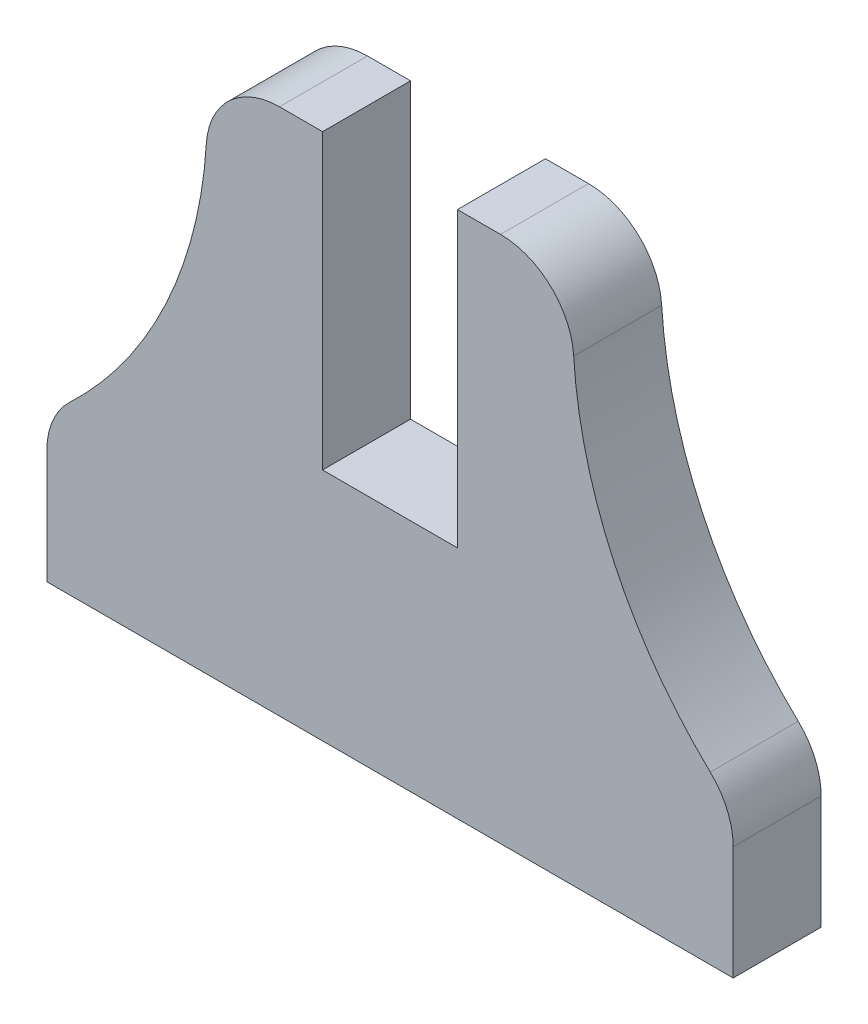
SolidWorks part; units mm, degrees
ref_plane "Front Plane" through (0, 0, 0) normal (0, 0, 1) x (1, 0, 0)
ref_plane "Top Plane" through (0, 0, 0) normal (0, 1, 0) x (1, 0, 0)
ref_plane "Right Plane" through (0, 0, 0) normal (1, 0, 0) x (0, 0, -1)
sketch "Sketch1" plane through (0, 0, 0) normal (0, 0, 1) x (1, 0, 0)
  line L0 (-4, -181.6843) -> (0, -181.6843) construction
  line L2 (-4.3, -163.6943) -> (-4.3, -173.6843)
  line L3 (-3.7, -181.6843) -> (-0.3, -181.6843)
  line L4 (0.3, -163.6943) -> (0.3, -173.6843)
  line L5 (-2, -163.6843) -> (-2, -121.6843) construction
  line L6 (-4, -121.6843) -> (0, -121.6843) construction
  line L7 (0, -171.6843) -> (0, -124.1843) construction
  line L8 (-0.3, -181.6843) -> (9.7, -181.6843)
  line L9 (0.3, -163.6943) -> (1.7677, -163.6943)
  line L10 (9.7, -181.6843) -> (9.7, -177.8097)
  line L11 (-13.7, -181.6843) -> (-13.7, -177.8097)
  line L12 (-4.3, -163.6943) -> (-5.7677, -163.6943)
  line L13 (-3.7, -181.6843) -> (-13.7, -181.6843)
  line L14 (-4.3, -173.6843) -> (0.3, -173.6843)
  arc A0 (4.2628, -166.0385) -> (8.9191, -175.9946) centre (19.2336, -165.1037) ccw
  arc A1 (9.7, -177.8097) -> (8.9191, -175.9946) centre (7.2, -177.8097) ccw
  arc A2 (1.7677, -163.6943) -> (4.2628, -166.0385) centre (1.7677, -166.1943) cw
  arc A3 (-5.7677, -163.6943) -> (-8.2628, -166.0385) centre (-5.7677, -166.1943) ccw
  arc A4 (-13.7, -177.8097) -> (-12.9191, -175.9946) centre (-11.2, -177.8097) cw
  arc A5 (-8.2628, -166.0385) -> (-12.9191, -175.9946) centre (-23.2336, -165.1037) cw
  point P18 (9.7, -176.6843)
  point P21 (4.3, -163.6943)
  point P30 (-8.3, -163.6943)
  point P31 (-13.7, -176.6843)
  point P37 (-2, -173.6843)
  dimension "D6" = 15
  dimension "D7" = 2.5
  dimension "D1" = 18
  dimension "D2" = 0.3
  dimension "D3" = 10
  dimension "D4" = 4
  dimension "D5" = 5
  dimension "D8" = 8
  dimension "D9" = 3.4
extrude "Boss-Extrude1" add sketch "Sketch1" along normal blind 3
